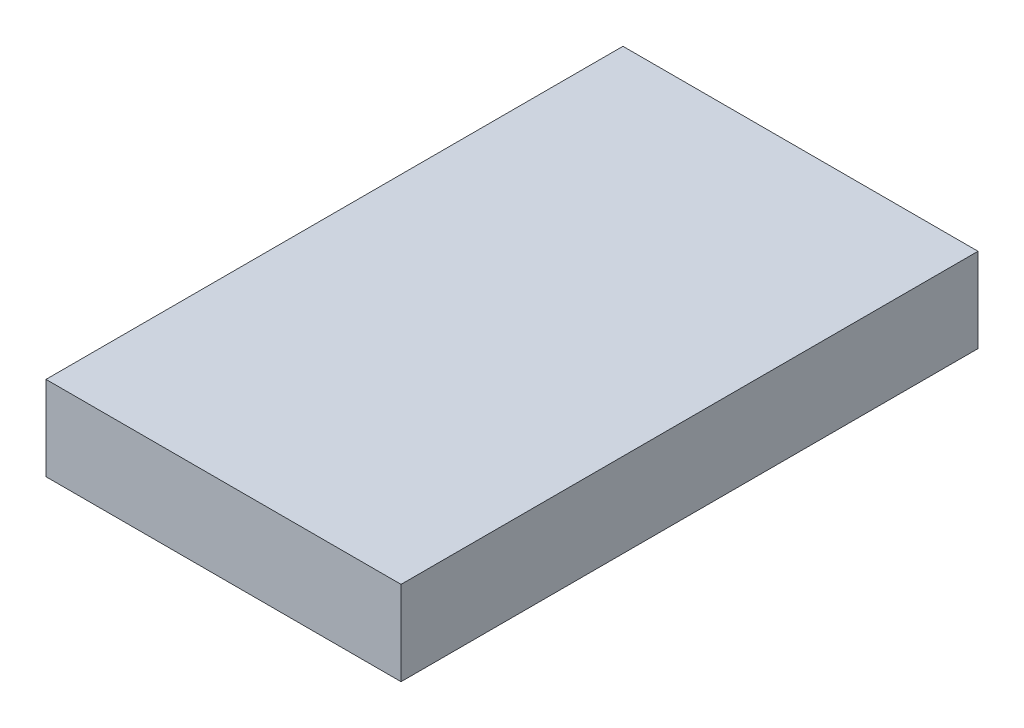
SolidWorks part; units mm, degrees
material "Nailon 101"
ref_plane "Alzado" through (0, 0, 0) normal (0, 0, 1) x (1, 0, 0)
ref_plane "Planta" through (0, 0, 0) normal (0, 1, 0) x (1, 0, 0)
ref_plane "Vista lateral" through (0, 0, 0) normal (1, 0, 0) x (0, 0, -1)
sketch "Croquis1" plane through (0, 0, 0) normal (0, 0, 1) x (1, 0, 0)
  line L1 (0, 0) -> (160, 0)
  line L2 (0, 0) -> (0, 38)
  line L3 (0, 38) -> (160, 38)
  line L4 (160, 0) -> (160, 38)
  dimension "D1" = 38
  dimension "D2" = 160
extrude "Saliente-Extruir1" add sketch "Croquis1" along normal blind 260
